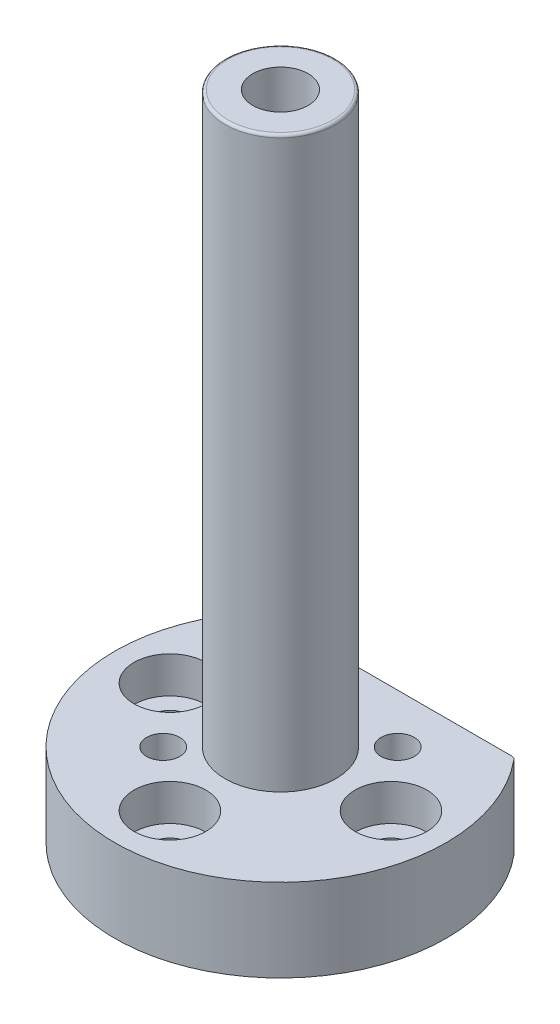
SolidWorks part; units mm, degrees
material "3003 Alloy"
ref_plane "Front Plane" through (0, 0, 0) normal (0, 0, 1) x (1, 0, 0)
ref_plane "Top Plane" through (0, 0, 0) normal (0, 1, 0) x (1, 0, 0)
ref_plane "Right Plane" through (0, 0, 0) normal (1, 0, 0) x (0, 0, -1)
sketch "Sketch1" plane through (0, 0, 0) normal (0, 1, 0) x (1, 0, 0)
  line L0 (22.798, 19.5) -> (-22.798, 19.5)
  arc A0 (-22.798, 19.5) -> (22.798, 19.5) centre (0, 0) ccw
  dimension "D1" = 60
  dimension "D2" = 19.5
extrude "Boss-Extrude1" add sketch "Sketch1" along normal blind 15
sketch "Sketch2" plane through (0, 15, 0) normal (0, 1, 0) x (1, 0, 0)
  circle A0 centre (0, 0) radius 10
  dimension "D1" = 20
extrude "Boss-Extrude2" add sketch "Sketch2" along normal blind 103
sketch "Sketch4" plane through (0, 0, 0) normal (0, -1, 0) x (1, 0, 0)
  circle A0 centre (0, 0) radius 7.25
  dimension "D1" = 14.5
extrude "Cut-Extrude1" cut sketch "Sketch4" against normal blind 57
sketch "Sketch5" plane through (0, 57, 0) normal (0, -1, 0) x (1, 0, 0)
  circle A0 centre (0, 0) radius 5
  dimension "D1" = 10
extrude "Cut-Extrude2" cut sketch "Sketch5" against normal through all
sketch "Sketch7" plane through (0, 15, 0) normal (0, 1, 0) x (1, 0, 0)
  circle A0 centre (0, -20) radius 6.5
  point P9 (0, 0)
  point P13 (0, 0)
  dimension "D2" = 13
  dimension "D1" = 20
extrude "Cut-Extrude3" cut sketch "Sketch7" against normal blind 6.6
sketch "Sketch8" plane through (0, 8.4, 0) normal (0, 1, 0) x (1, 0, 0)
  circle A0 centre (0, -20) radius 3.3
  dimension "D1" = 6.6
extrude "Cut-Extrude4" cut sketch "Sketch8" against normal through all
pattern_circular "CirPattern1" count 4 over 360 about axis through (0, 0, 0) along (0, 1, 0) skipping 2 of "Cut-Extrude4", "Cut-Extrude3"
fillet "Fillet1" radius 0.5 1 edges at (0, 118, 10)
fillet "Fillet2" radius 1 2 edges at (22.798, 7.5, -19.5) (-22.798, 7.5, -19.5)
sketch "Sketch9" plane through (0, 15, 0) normal (0, 1, 0) x (1, 0, 0)
  line L0 (10.6066, 10.6066) -> (0, 0) construction
  line L1 (0, 0) -> (-10.6066, -10.6066) construction
  line L2 (0, 0) -> (20, 0) construction
  circle A0 centre (-10.6066, -10.6066) radius 3
  circle A1 centre (10.6066, 10.6066) radius 3
  arc A2 (-23.1028, 19.1379) -> (23.1028, 19.1379) centre (0, 0) ccw construction
  dimension "D1" = 6
  dimension "D2" = 6
  dimension "D3" = 15
  dimension "D4" = 15
  dimension "D5" = 45
extrude "Cut-Extrude5" cut sketch "Sketch9" against normal through all
